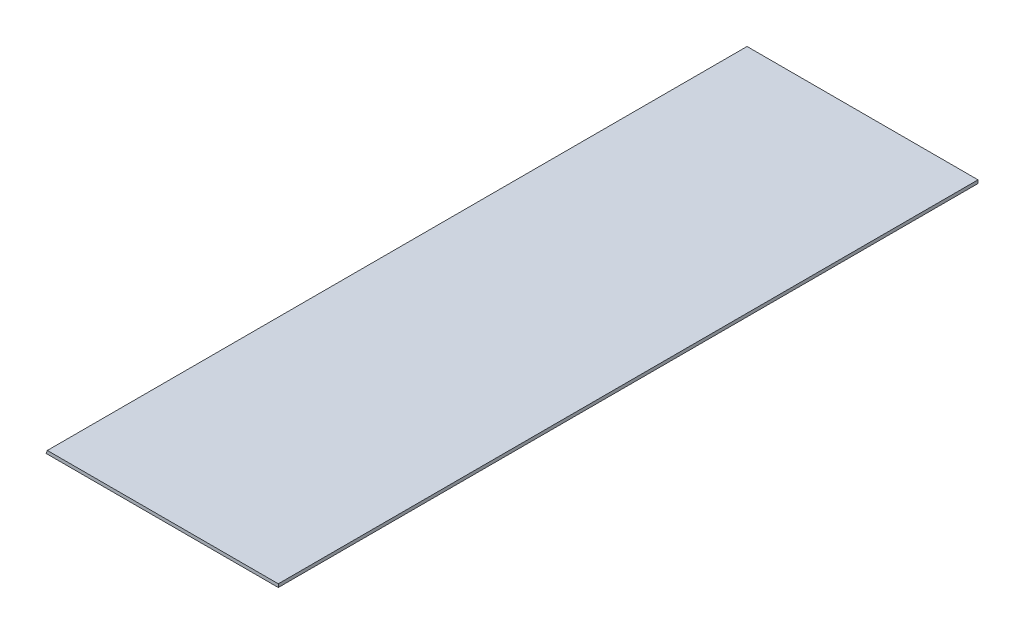
SolidWorks part; units mm, degrees
ref_plane "Front Plane" through (0, 0, 0) normal (0, 0, 1) x (1, 0, 0)
ref_plane "Top Plane" through (0, 0, 0) normal (0, 1, 0) x (1, 0, 0)
ref_plane "Right Plane" through (0, 0, 0) normal (1, 0, 0) x (0, 0, -1)
sketch "Sketch1" plane through (0, 0, 0) normal (0, 0, 1) x (1, 0, 0)
  line L0 (0, 0) -> (0.9785, 2.3622)
  line L1 (0.9785, 2.3622) -> (168.656, 2.3622)
  line L2 (168.656, 2.3622) -> (168.656, 0)
  line L3 (168.656, 0) -> (0, 0)
  dimension "D1" = 67.5
  dimension "D2" = 2.3622
  dimension "D3" = 168.656
extrude "Boss-Extrude1" add sketch "Sketch1" along normal blind 508
